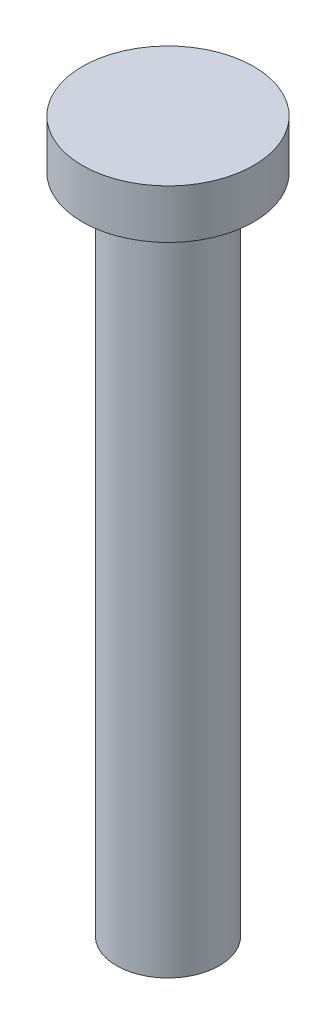
SolidWorks part; units mm, degrees
ref_plane "Front Plane" through (0, 0, 0) normal (0, 0, 1) x (1, 0, 0)
ref_plane "Top Plane" through (0, 0, 0) normal (0, 1, 0) x (1, 0, 0)
ref_plane "Right Plane" through (0, 0, 0) normal (1, 0, 0) x (0, 0, -1)
sketch "Sketch1" plane through (0, 0, 0) normal (0, 1, 0) x (1, 0, 0)
  circle A0 centre (0, 0) radius 2.1
  dimension "D1" = 4.2
extrude "Boss-Extrude1" add sketch "Sketch1" along normal blind 27
sketch "Sketch2" plane through (0, 27, 0) normal (0, 1, 0) x (1, 0, 0)
  circle A0 centre (0, 0) radius 3.5
  dimension "D1" = 7
extrude "Boss-Extrude3" add sketch "Sketch2" along normal blind 2
